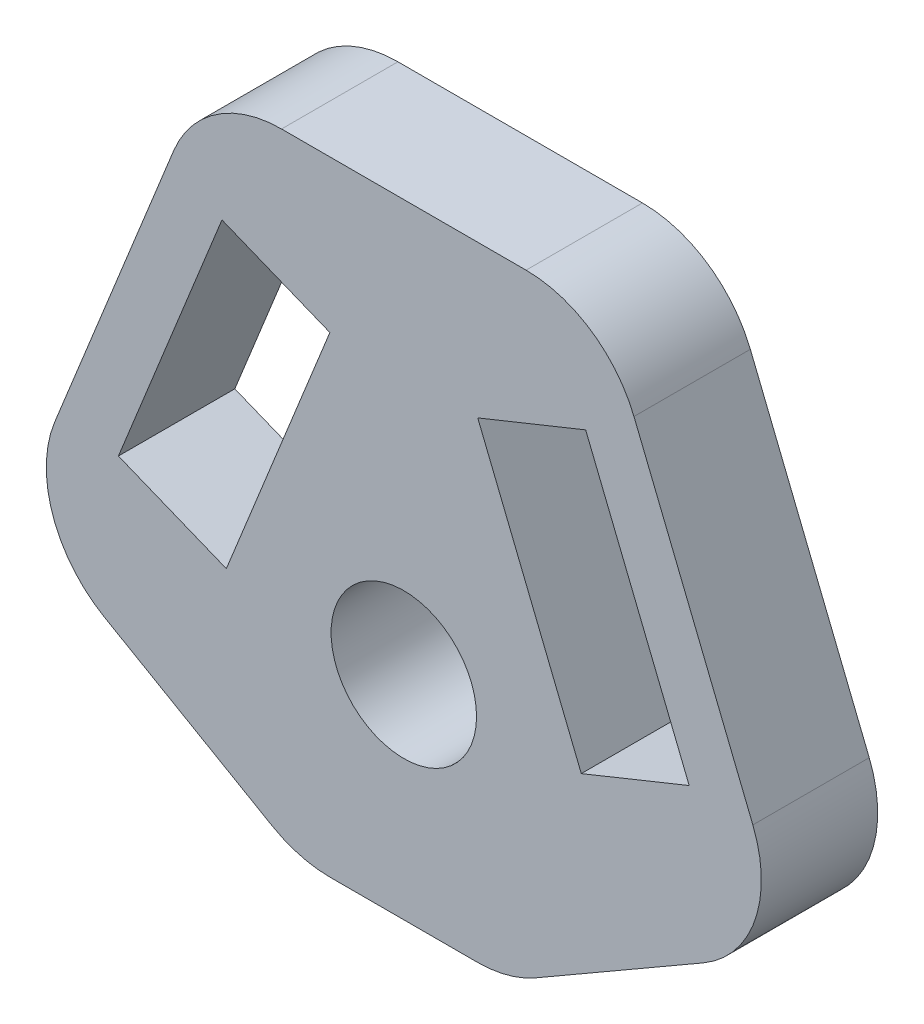
SolidWorks part; units mm, degrees
ref_plane "正面" through (0, 0, 0) normal (0, 0, 1) x (1, 0, 0)
ref_plane "平面" through (0, 0, 0) normal (0, 1, 0) x (1, 0, 0)
ref_plane "右側面" through (0, 0, 0) normal (1, 0, 0) x (0, 0, -1)
sketch "ｽｹｯﾁ1" plane through (0, 0, 0) normal (0, 0, 1) x (1, 0, 0)
  line L0 (0, 0) -> (0, 14.1393) construction
  line L1 (-6.9, 14.1393) -> (6.9, 14.1393)
  line L2 (6.9, 14.1393) -> (13.2995, -1.7)
  line L3 (13.2995, -1.7) -> (3.6, -7.3)
  line L4 (3.6, -7.3) -> (-3.6, -7.3)
  line L5 (2.5412, 8.9108) -> (6.25, 10.4092)
  line L6 (6.25, 10.4092) -> (9.8087, 1.601)
  line L7 (9.8087, 1.601) -> (6.1, 0.1025)
  line L8 (6.1, 0.1025) -> (2.5412, 8.9108)
  line L9 (-6.1, 0.1025) -> (-2.5412, 8.9108)
  line L10 (-9.8087, 1.601) -> (-6.1, 0.1025)
  line L11 (-6.25, 10.4092) -> (-9.8087, 1.601)
  line L12 (-2.5412, 8.9108) -> (-6.25, 10.4092)
  line L13 (-13.2995, -1.7) -> (-3.6, -7.3)
  line L14 (-6.9, 14.1393) -> (-13.2995, -1.7)
  circle A0 centre (0, 0) radius 2.5
  point P12 (13.5385, -2.1038)
  point P13 (0, 0)
  point P14 (8.0279, 13.8003)
  point P15 (12.9805, -1.4063)
  point P16 (5.9392, 0)
  point P17 (13.2995, -1.6852)
  point P23 (0, -7.3)
  dimension "D1" = 5
  dimension "D2" = 22
  dimension "D3" = 4
  dimension "D4" = 2
  dimension "D5" = 9.5
  dimension "D6" = 6.9
  dimension "D7" = 3.6
  dimension "D8" = 11.2
  dimension "D9" = 150
  dimension "D10" = 7.3
  dimension "D11" = 6.1
extrude "ﾎﾞｽ - 押し出し1" add sketch "ｽｹｯﾁ1" along normal blind 4
fillet "ﾌｨﾚｯﾄ1" radius 4 6 edges at (3.6, -7.3, 2) (-3.6, -7.3, 2) (-13.2995, -1.7, 2) (13.2995, -1.7, 2) (-6.9, 14.1393, 2) (6.9, 14.1393, 2)
